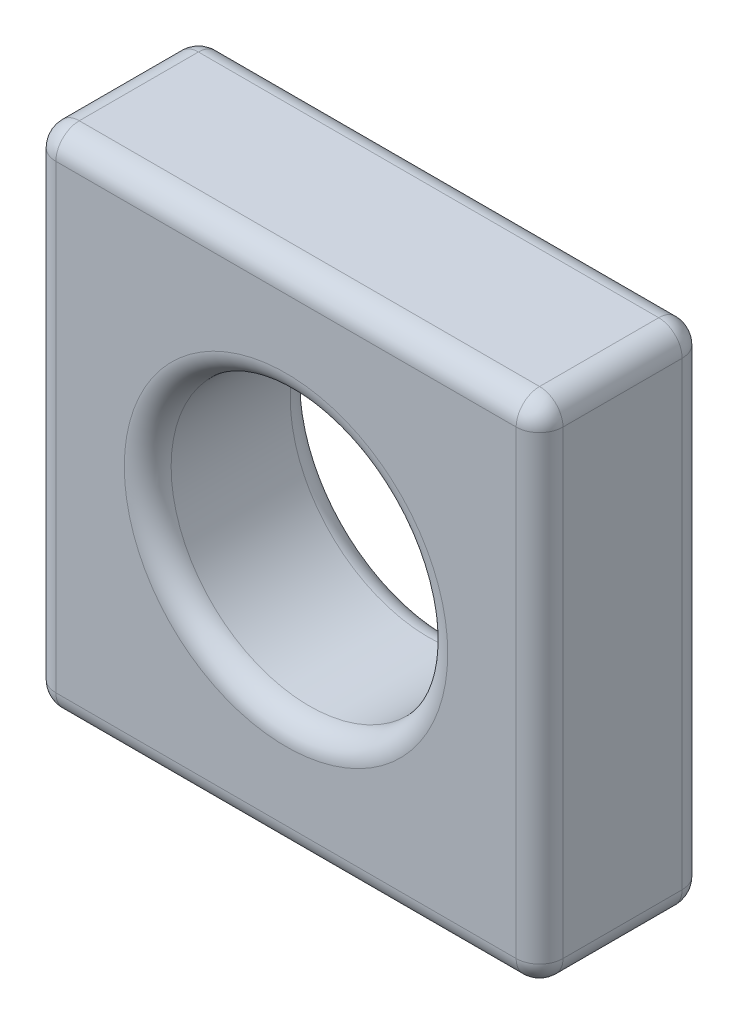
SolidWorks part; units mm, degrees
ref_plane "Front Plane" through (0, 0, 0) normal (0, 0, 1) x (1, 0, 0)
ref_plane "Top Plane" through (0, 0, 0) normal (0, 1, 0) x (1, 0, 0)
ref_plane "Right Plane" through (0, 0, 0) normal (1, 0, 0) x (0, 0, -1)
sketch "Sketch1" plane through (0, 0, 0) normal (0, 0, 1) x (1, 0, 0)
  line L0 (2.75, 5.5) -> (2.75, 2.75) construction
  line L1 (0, 0) -> (5.5, 0)
  line L2 (0, 0) -> (0, 5.5)
  line L3 (0, 5.5) -> (5.5, 5.5)
  line L4 (5.5, 0) -> (5.5, 5.5)
  line L5 (2.75, 2.75) -> (0, 2.75) construction
  circle A0 centre (2.75, 2.75) radius 1.5
  dimension "D2" = 3
  dimension "D1" = 5.5
extrude "Boss-Extrude1" add sketch "Sketch1" along normal blind 1.8
fillet "Fillet1" radius 0.254 14 edges at (2.75, 5.5, 1.8) (5.5, 2.75, 1.8) (2.75, 0, 1.8) (0, 2.75, 1.8) (2.75, 0, 0) (5.5, 2.75, 0) (2.75, 5.5, 0) (0, 2.75, 0) (5.5, 0, 0.9) (0, 0, 0.9) (0, 5.5, 0.9) (5.5, 5.5, 0.9) (4.25, 2.75, 0) (4.25, 2.75, 1.8)
